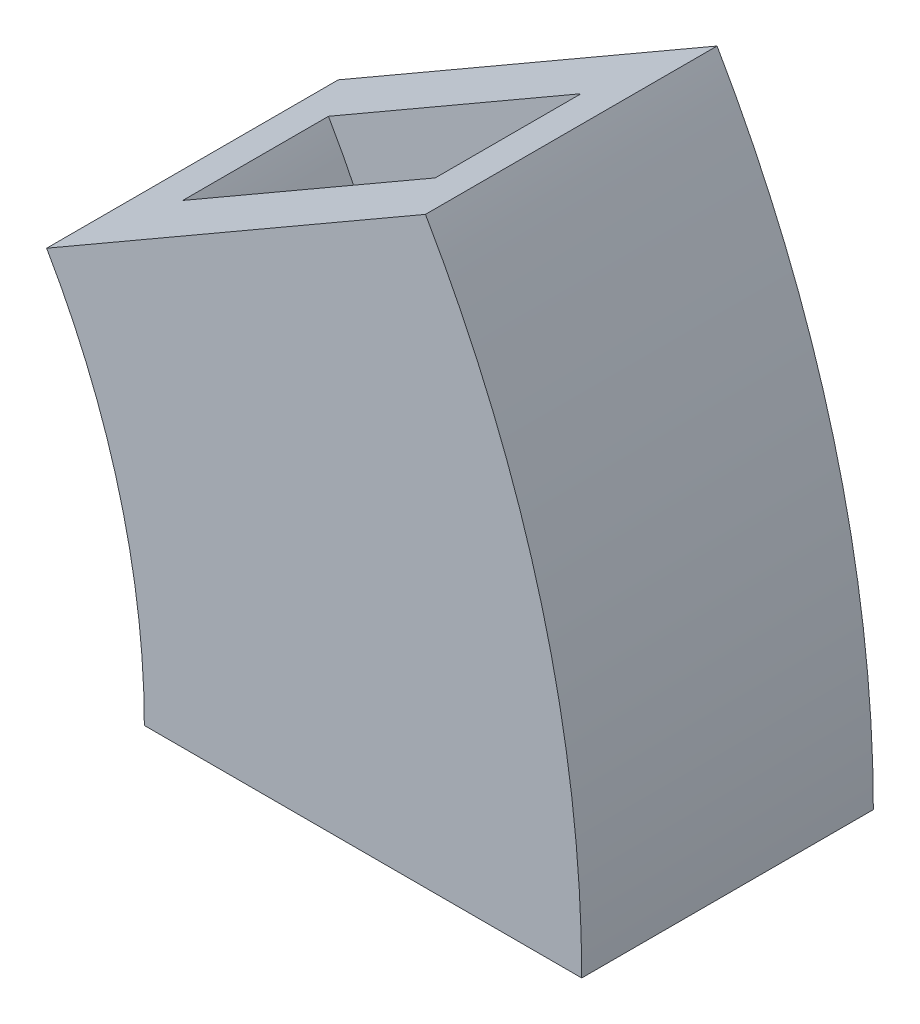
SolidWorks part; units mm, degrees
ref_plane "Front Plane" through (0, 0, 0) normal (0, 0, 1) x (1, 0, 0)
ref_plane "Top Plane" through (0, 0, 0) normal (0, 1, 0) x (1, 0, 0)
ref_plane "Right Plane" through (0, 0, 0) normal (1, 0, 0) x (0, 0, -1)
sketch "Sketch1" plane through (0, 0, 0) normal (0, 0, 1) x (1, 0, 0)
  line L0 (-7.2376, 15.2484) -> (72.7624, 15.2484)
  line L1 (-7.2376, 15.2484) -> (-87.2376, 15.2484)
  line L2 (-7.2376, 15.2484) -> (62.0444, 55.2484)
  circle A0 centre (-7.2376, 15.2484) radius 50
  circle A1 centre (-7.2376, 15.2484) radius 55
  circle A2 centre (-7.2376, 15.2484) radius 75
  circle A3 centre (-7.2376, 15.2484) radius 80
  arc A4 (-87.2376, 15.2484) -> (62.0444, 55.2484) centre (-7.2376, 15.2484) cw
extrude "Boss-Extrude1" add sketch "Sketch1" along normal blind 10 contours L0 A1 L2 A0 | L0 A3 L2 A2
sketch "Sketch2" plane through (0, 0, 10) normal (0, 0, 1) x (1, 0, 0)
  line L0 (36.0637, 40.2484) -> (62.0444, 55.2484)
  line L1 (42.7624, 15.2484) -> (72.7624, 15.2484)
  arc A0 (36.0637, 40.2484) -> (42.7624, 15.2484) centre (-7.2376, 15.2484) cw
  arc A1 (62.0444, 55.2484) -> (72.7624, 15.2484) centre (-7.2376, 15.2484) cw
extrude "Boss-Extrude2" add sketch "Sketch2" along normal blind 5
sketch "Sketch3" plane through (0, 0, 0) normal (0, 0, -1) x (-1, 0, 0)
  line L0 (-36.0637, 40.2484) -> (-62.0444, 55.2484)
  line L1 (-42.7624, 15.2484) -> (-72.7624, 15.2484)
  arc A0 (-72.7624, 15.2484) -> (-62.0444, 55.2484) centre (7.2376, 15.2484) cw
  arc A1 (-36.0637, 40.2484) -> (-42.7624, 15.2484) centre (7.2376, 15.2484) ccw
extrude "Boss-Extrude3" add sketch "Sketch3" along normal blind 5
